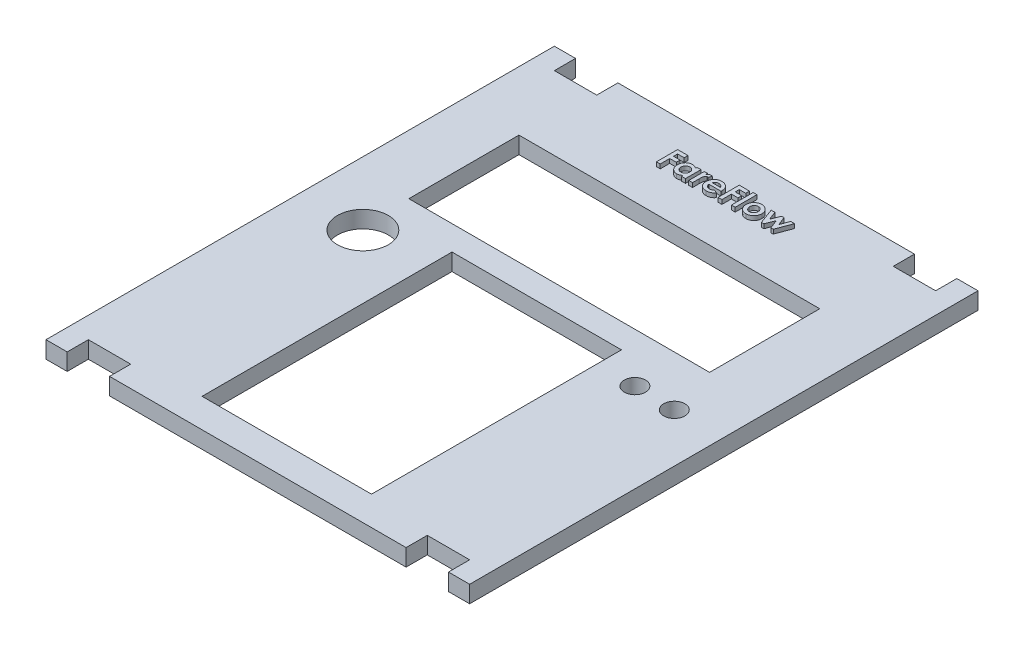
SolidWorks part; units mm, degrees
ref_plane "Front Plane" through (0, 0, 0) normal (0, 0, 1) x (1, 0, 0)
ref_plane "Top Plane" through (0, 0, 0) normal (0, 1, 0) x (1, 0, 0)
ref_plane "Right Plane" through (0, 0, 0) normal (1, 0, 0) x (0, 0, -1)
sketch "Sketch1" plane through (0, 0, 0) normal (0, 1, 0) x (1, 0, 0)
  line L1 (-50, 60) -> (50, 60)
  line L2 (-50, 60) -> (-50, -60)
  line L3 (-50, -60) -> (50, -60)
  line L4 (50, 60) -> (50, -60)
  line L5 (-50, 60) -> (50, -60) construction
  line L6 (-50, -60) -> (50, 60) construction
  point P0 (0, 0)
  dimension "D1" = 100
  dimension "D2" = 120
extrude "Boss-Extrude1" add sketch "Sketch1" along normal blind 4
sketch "Sketch3" plane through (0, 4, 0) normal (0, 1, 0) x (1, 0, 0)
  line L0 (0, 52.9719) -> (0, -56.6505) construction
  line L1 (50, 60) -> (-50, 60) construction
  line L2 (-58.2875, 0) -> (59.2955, 0) construction
  line L3 (50, -60) -> (50, 60) construction
  line L4 (-36, 37.6445) -> (35, 37.6445)
  line L5 (-36, 37.6445) -> (-36, 11.6445)
  line L6 (-36, 11.6445) -> (35, 11.6445)
  line L7 (35, 37.6445) -> (35, 11.6445)
  line L12 (-20, 5.8376) -> (20, 5.8376)
  line L13 (-20, 5.8376) -> (-20, -53.1624)
  line L14 (-20, -53.1624) -> (20, -53.1624)
  line L15 (20, 5.8376) -> (20, -53.1624)
  line L16 (-45, 60) -> (-35, 60)
  line L17 (-45, 60) -> (-45, 55)
  line L18 (-45, 55) -> (-35, 55)
  line L19 (-35, 60) -> (-35, 55)
  line L21 (-50, 60) -> (-50, -60) construction
  line L22 (-50, -60) -> (50, -60) construction
  line L23 (35, 60) -> (45, 60)
  line L24 (35, 60) -> (35, 55)
  line L25 (35, 55) -> (45, 55)
  line L26 (45, 60) -> (45, 55)
  line L27 (-45, -55) -> (-35, -55)
  line L28 (-45, -55) -> (-45, -60)
  line L29 (-45, -60) -> (-35, -60)
  line L30 (-35, -55) -> (-35, -60)
  line L32 (35, -55) -> (45, -55)
  line L33 (35, -55) -> (35, -60)
  line L34 (35, -60) -> (45, -60)
  line L35 (45, -55) -> (45, -60)
  circle A0 centre (-35, -0.1976) radius 6
  circle A1 centre (29, 0.0113) radius 2.5
  circle A3 centre (38.5, -0.1898) radius 2.5
  point P33 (45, 57.5)
  dimension "D7" = 9.5
  dimension "D8" = 9
  dimension "D1" = 71
  dimension "D2" = 26
  dimension "D3" = 15
  dimension "D4" = 59
  dimension "D5" = 40
  dimension "D6" = 30
  dimension "D9" = 15
  dimension "D10" = 5
  dimension "D11" = 10
  dimension "D12" = 5
  dimension "D13" = 5
  dimension "D14" = 10
  dimension "D15" = 5
  dimension "D16" = 5
  dimension "D17" = 10
  dimension "D18" = 5
  dimension "D19" = 5
  dimension "D20" = 5
  dimension "D21" = 10
extrude "Cut-Extrude1" cut sketch "Sketch3" against normal through all
sketch "Sketch4" plane through (0, 4, 0) normal (0, 1, 0) x (1, 0, 0)
  text T0 "<b>FareFlow</b>" font "Century Gothic" height 5
extrude "Boss-Extrude2" add sketch "Sketch4" along normal blind 1
